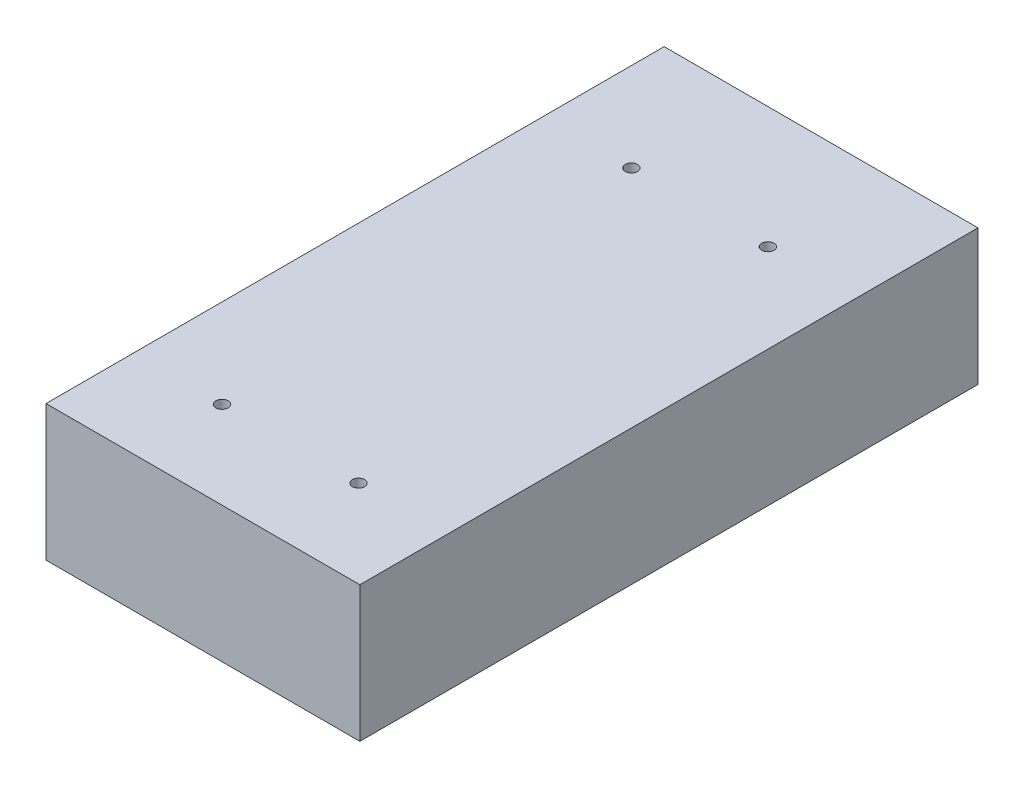
SolidWorks part; units mm, degrees
other "Camera1"
ref_plane "Front Plane" through (0, 0, 0) normal (0, 0, 1) x (1, 0, 0)
ref_plane "Top Plane" through (0, 0, 0) normal (0, 1, 0) x (1, 0, 0)
ref_plane "Right Plane" through (0, 0, 0) normal (1, 0, 0) x (0, 0, -1)
sketch "Sketch3" plane through (0, 0, 0) normal (0, 1, 0) x (1, 0, 0)
  line L1 (0, 0) -> (115, 0)
  line L2 (0, 0) -> (0, 226.5)
  line L3 (0, 226.5) -> (115, 226.5)
  line L4 (115, 0) -> (115, 226.5)
  dimension "D1" = 226.5
  dimension "D2" = 115
extrude "Boss-Extrude1" add sketch "Sketch3" along normal blind 49.7
hole_wizard "CSK for M4 Flat Head Machine Screw2" positions "Sketch7" profile "Sketch6" countersink size "M4" standard "ANSI Metric" end condition through all
sketch "Sketch7" plane through (0, 0, 0) normal (0, -1, 0) x (-1, 0, 0)
  line L0 (0, 0) -> (-115, 0) construction
  line L1 (-57.5, 0) -> (-57.5, 226.5) construction
  line L2 (-115, 226.5) -> (0, 226.5) construction
  line L4 (0, 226.5) -> (0, 0) construction
  line L5 (-115, 0) -> (-115, 226.5) construction
  point P0 (-32.5, 32)
  point P2 (-82.5, 32)
  point P4 (-82.5, 182)
  point P6 (-32.5, 182)
  dimension "D1" = 50
  dimension "D2" = 32
  dimension "D3" = 150
sketch "Sketch6" plane through (32.5, 0, -32) normal (1, 0, 0) x (0, 0, -1)
  line L0 (0, 0) -> (0, 49.7)
  line L1 (0, 49.7) -> (2.25, 49.7)
  line L2 (2.25, 49.7) -> (2.25, 2.45)
  line L3 (2.25, 2.45) -> (4.7, 0)
  line L5 (4.7, 0) -> (0, 0)
  line L6 (-2.25, 2.45) -> (-4.7, 0) construction
  line L11 (0, -6.35) -> (0, 107.95) construction
  dimension "Thru Hole Dia." = 4.5
  dimension "Thru Hole Depth" = 49.7
  dimension "Near C'Sink Dia." = 9.4
  dimension "Near C'Sink Angle" = 90
sketch "Sketch8" plane through (0, 0, 0) normal (0, -1, 0) x (-1, 0, 0)
  line L0 (-1.2963, 226.5) -> (-1.2963, 207.9168)
  line L1 (-115, 226.5) -> (0, 226.5) construction
  line L2 (-1.2963, 207.9168) -> (-113.7407, 207.9168)
  line L3 (-113.7407, 207.9168) -> (-113.7407, 226.5)
  line L4 (-113.7407, 226.5) -> (-1.2963, 226.5)
extrude "Cut-Extrude1" cut sketch "Sketch8" against normal blind 48
sketch "Sketch9" plane through (0, 0, 0) normal (0, -1, 0) x (-1, 0, 0)
  circle A0 centre (-49.003, 66.5469) radius 19.2623 construction
  circle A1 centre (-49.003, 66.5469) radius 26.6156 construction
  arc A2 (-29.7407, 66.5469) -> (-36.3737, 52.0026) centre (-49.003, 66.5469) cw construction
  arc A3 (-35.2416, 50.6988) -> (-28.0139, 66.5469) centre (-49.003, 66.5469) ccw
  arc A4 (-37.5058, 53.3064) -> (-31.4674, 66.5469) centre (-49.003, 66.5469) ccw
  arc A5 (-37.5058, 53.3064) -> (-35.2416, 50.6988) centre (-36.3737, 52.0026) ccw
  arc A6 (-28.0139, 66.5469) -> (-31.4674, 66.5469) centre (-29.7407, 66.5469) ccw
  arc A7 (-49.003, 47.2846) -> (-61.6323, 52.0026) centre (-49.003, 66.5469) cw construction
  arc A8 (-62.8151, 50.6403) -> (-49.003, 45.4805) centre (-49.003, 66.5469) ccw
  arc A9 (-60.4494, 53.3648) -> (-49.003, 49.0887) centre (-49.003, 66.5469) ccw
  arc A10 (-60.4494, 53.3648) -> (-62.8151, 50.6403) centre (-61.6323, 52.0026) ccw
  arc A11 (-49.003, 45.4805) -> (-49.003, 49.0887) centre (-49.003, 47.2846) ccw
  arc A12 (-68.2653, 66.5469) -> (-66.594, 74.3952) centre (-49.003, 66.5469) cw construction
  arc A13 (-68.5722, 75.2777) -> (-70.4315, 66.5469) centre (-49.003, 66.5469) ccw
  arc A14 (-64.6158, 73.5126) -> (-66.0992, 66.5469) centre (-49.003, 66.5469) ccw
  arc A15 (-64.6158, 73.5126) -> (-68.5722, 75.2777) centre (-66.594, 74.3952) ccw
  arc A16 (-70.4315, 66.5469) -> (-66.0992, 66.5469) centre (-68.2653, 66.5469) ccw
  arc A17 (-36.3737, 81.0913) -> (-49.003, 85.8093) centre (-49.003, 66.5469) ccw construction
  arc A18 (-35.2586, 82.3755) -> (-49.003, 87.51) centre (-49.003, 66.5469) ccw
  arc A19 (-37.4888, 79.8071) -> (-49.003, 84.1085) centre (-49.003, 66.5469) ccw
  arc A20 (-37.4888, 79.8071) -> (-35.2586, 82.3755) centre (-36.3737, 81.0913) ccw
  arc A21 (-49.003, 87.51) -> (-49.003, 84.1085) centre (-49.003, 85.8093) ccw
  arc A22 (-49.003, 39.9314) -> (-68.2653, 48.1798) centre (-49.003, 66.5469) cw construction
  arc A23 (-69.4031, 47.0949) -> (-49.003, 38.3593) centre (-49.003, 66.5469) ccw
  arc A24 (-67.1276, 49.2647) -> (-49.003, 41.5035) centre (-49.003, 66.5469) ccw
  arc A25 (-67.1276, 49.2647) -> (-69.4031, 47.0949) centre (-68.2653, 48.1798) ccw
  arc A26 (-49.003, 38.3593) -> (-49.003, 41.5035) centre (-49.003, 39.9314) ccw
  arc A27 (-73.7478, 56.7448) -> (-75.1112, 71.7188) centre (-49.003, 66.5469) cw construction
  arc A28 (-76.9557, 72.0842) -> (-75.496, 56.0523) centre (-49.003, 66.5469) ccw
  arc A29 (-73.2668, 71.3535) -> (-71.9997, 57.4373) centre (-49.003, 66.5469) ccw
  arc A30 (-73.2668, 71.3535) -> (-76.9557, 72.0842) centre (-75.1112, 71.7188) ccw
  arc A31 (-75.496, 56.0523) -> (-71.9997, 57.4373) centre (-73.7478, 56.7448) ccw
  arc A32 (-70.4315, 82.3333) -> (-60.4494, 90.5754) centre (-49.003, 66.5469) cw construction
  arc A33 (-61.4795, 92.7378) -> (-72.3598, 83.7539) centre (-49.003, 66.5469) ccw
  arc A34 (-59.4193, 88.4131) -> (-68.5031, 80.9127) centre (-49.003, 66.5469) ccw
  arc A35 (-59.4193, 88.4131) -> (-61.4795, 92.7378) centre (-60.4494, 90.5754) ccw
  arc A36 (-72.3598, 83.7539) -> (-68.5031, 80.9127) centre (-70.4315, 82.3333) ccw
  arc A37 (-46.3263, 93.0276) -> (-31.4674, 86.5692) centre (-49.003, 66.5469) cw construction
  arc A38 (-30.0446, 88.1937) -> (-46.1091, 95.1761) centre (-49.003, 66.5469) ccw
  arc A39 (-32.8901, 84.9447) -> (-46.5435, 90.8791) centre (-49.003, 66.5469) ccw
  arc A40 (-32.8901, 84.9447) -> (-30.0446, 88.1937) centre (-31.4674, 86.5692) ccw
  arc A41 (-46.1091, 95.1761) -> (-46.5435, 90.8791) centre (-46.3263, 93.0276) ccw
  arc A42 (-23.3151, 73.5126) -> (-23.9949, 57.4373) centre (-49.003, 66.5469) cw construction
  arc A43 (-22.2427, 56.799) -> (-21.5152, 74.0007) centre (-49.003, 66.5469) ccw
  arc A44 (-25.7472, 58.0756) -> (-25.1149, 73.0245) centre (-49.003, 66.5469) ccw
  arc A45 (-25.7472, 58.0756) -> (-22.2427, 56.799) centre (-23.9949, 57.4373) ccw
  arc A46 (-21.5152, 74.0007) -> (-25.1149, 73.0245) centre (-23.3151, 73.5126) ccw
  arc A47 (-29.7407, 48.1798) -> (-39.9912, 41.5035) centre (-49.003, 66.5469) cw construction
  arc A48 (-39.3014, 39.5866) -> (-28.2663, 46.774) centre (-49.003, 66.5469) ccw
  arc A49 (-40.681, 43.4203) -> (-31.215, 49.5856) centre (-49.003, 66.5469) ccw
  arc A50 (-40.681, 43.4203) -> (-39.3014, 39.5866) centre (-39.9912, 41.5035) ccw
  arc A51 (-28.2663, 46.774) -> (-31.215, 49.5856) centre (-29.7407, 48.1798) ccw
  point P0 (-29.7407, 66.5469)
  point P4 (-36.3737, 52.0026)
  point P5 (-61.6323, 52.0026)
  point P6 (-66.594, 74.3952)
  point P7 (-36.3737, 81.0913)
  point P11 (-31.4772, 58.5542)
  point P19 (-55.7439, 48.5026)
  point P24 (-67.8429, 70.5591)
  point P32 (-42.2621, 84.5913)
  point P40 (-59.48, 42.0802)
  point P48 (-75.5089, 64.1336)
  point P56 (-65.9492, 87.0705)
  point P64 (-38.3935, 90.9565)
  point P72 (-22.4112, 65.4224)
  point P80 (-34.4772, 44.2447)
extrude "Cut-Extrude2" cut sketch "Sketch9" against normal blind 6
hole_wizard "M4 Clearance Hole1" positions "Sketch11" profile "Sketch10" hole size "M4" standard "ANSI Metric"
sketch "Sketch11" plane through (0, 0, 0) normal (-1, 0, 0) x (0, 0, 1)
  line L0 (0, 49.7) -> (0, 0) construction
  line L2 (-226.5, 0) -> (0, 0) construction
  point P0 (-32.5, 37)
  point P2 (-182.5, 37)
  dimension "D1" = 32.5
  dimension "D2" = 37
  dimension "D3" = 150
sketch "Sketch10" plane through (0, 37, -32.5) normal (0, 1, 0) x (0, 0, 1)
  line L0 (0, 0) -> (0, 6.3519)
  line L1 (0, 6.3519) -> (2.25, 5)
  line L2 (2.25, 5) -> (2.25, 0)
  line L5 (2.25, 0) -> (0, 0)
  line L10 (0, 6.3519) -> (-2.25, 5) construction
  line L11 (0, -6.35) -> (0, 107.95) construction
  dimension "Hole Dia." = 4.5
  dimension "Hole Depth" = 5
  dimension "Drill Angle" = 118
